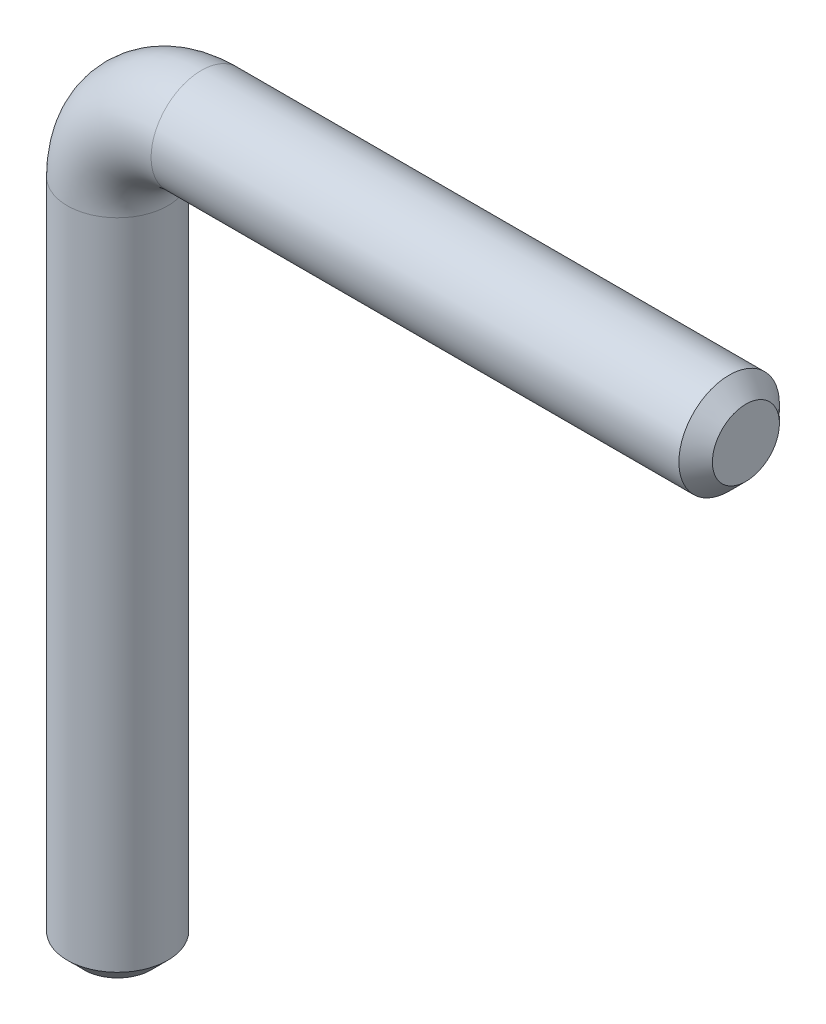
SolidWorks part; units mm, degrees
material "AISI 1020"
ref_plane "Front Plane" through (0, 0, 0) normal (0, 0, 1) x (1, 0, 0)
ref_plane "Top Plane" through (0, 0, 0) normal (0, 1, 0) x (1, 0, 0)
ref_plane "Right Plane" through (0, 0, 0) normal (1, 0, 0) x (0, 0, -1)
sketch "Sketch1" plane through (0, 0, 0) normal (0, 0, 1) x (1, 0, 0)
  line L0 (75, 90) -> (10, 90)
  line L1 (0, 80) -> (0, 0)
  arc A0 (10, 90) -> (0, 80) centre (10, 80) ccw
  dimension "D3" = 10
  dimension "D1" = 90
  dimension "D2" = 75
sweep "Sweep1" add path "Sketch1" circular profile diameter 12 parameters "D3"=12
chamfer "Chamfer1" distance 2 angle 45 2 edges at (75, 96, 0) (-6, 0, 0)
